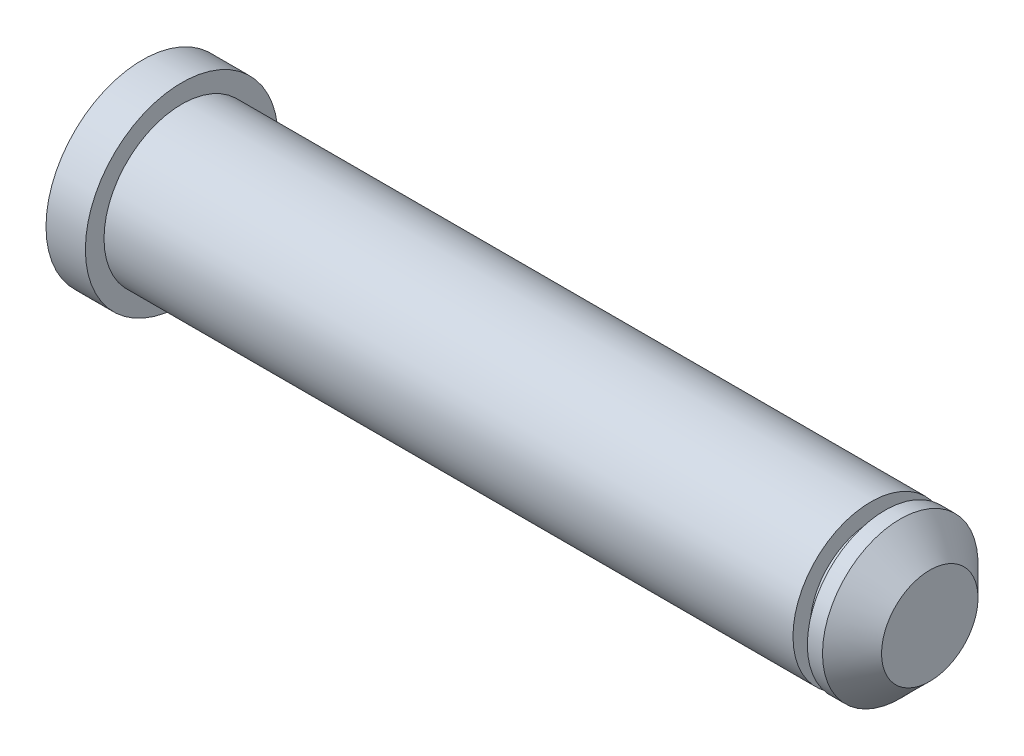
SolidWorks part; units mm, degrees
material "Stainless Steel (ferritic)"
ref_plane "Front" through (0, 0, 0) normal (0, 0, 1) x (1, 0, 0)
ref_plane "Top" through (0, 0, 0) normal (0, 1, 0) x (1, 0, 0)
ref_plane "Right" through (0, 0, 0) normal (1, 0, 0) x (0, 0, -1)
sketch "Sketch1" plane through (0, 0, 0) normal (0, 0, 1) x (1, 0, 0)
  line L0 (0, 0) -> (66.4337, 0) construction
  line L1 (0, 0) -> (0, 4.8966)
  line L2 (0, 4.8966) -> (2, 4.8966)
  line L3 (2, 4.8966) -> (2, 3.95)
  line L4 (2, 3.95) -> (37, 3.95)
  line L5 (37, 3.95) -> (37, 3.08)
  line L6 (37, 3.08) -> (37.73, 3.08)
  line L7 (37.73, 3.08) -> (37.73, 3.95)
  line L8 (37.73, 3.95) -> (38.5, 3.95)
  line L9 (40, 2.45) -> (40, 0)
  line L10 (0, 0) -> (40, 0)
  line L11 (38.5, 3.95) -> (40, 2.45)
  point P11 (40, 3.95)
  dimension "D1" = 1.5
  dimension "D2" = 7.9
  dimension "D3" = 2
  dimension "D4" = 0.73
  dimension "D5" = 6.16
  dimension "D6" = 35
  dimension "D7" = 40
  dimension "D8" = 45
revolve "Revolve1" add sketch "Sketch1" angle 360 about L0
